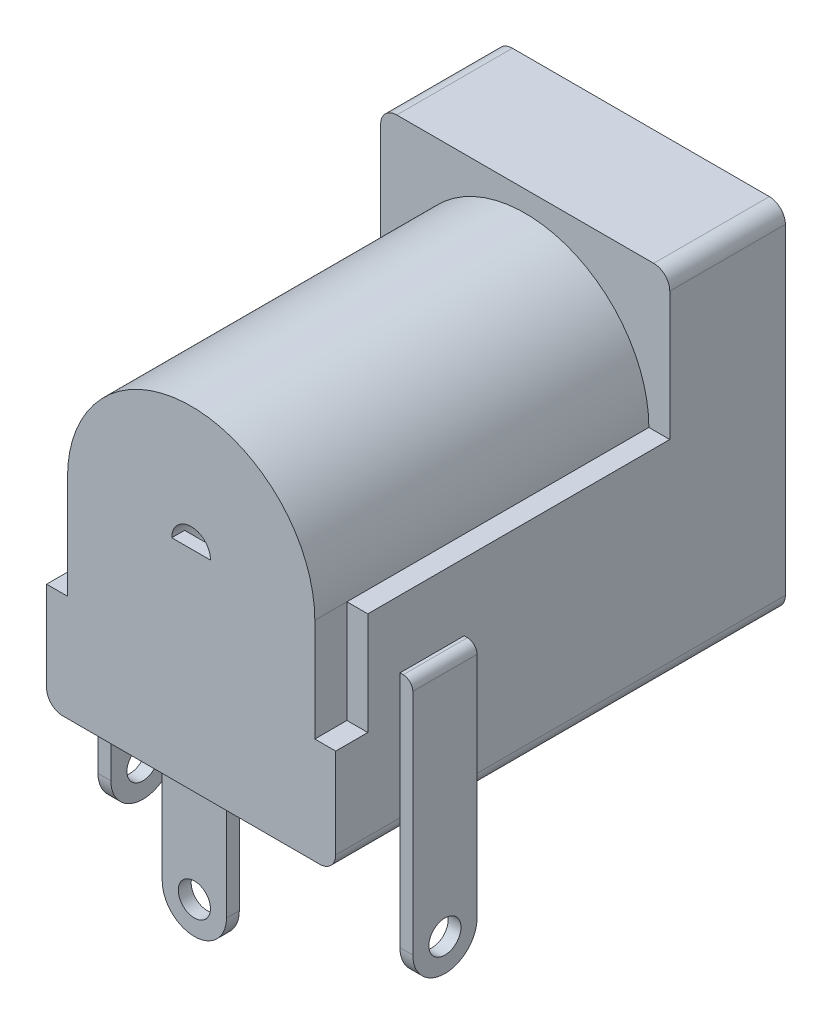
SolidWorks part; units mm, degrees
ref_plane "Front" through (0, 0, 0) normal (0, 0, 1) x (1, 0, 0)
ref_plane "Top" through (0, 0, 0) normal (0, 1, 0) x (1, 0, 0)
ref_plane "Right" through (0, 0, 0) normal (1, 0, 0) x (0, 0, -1)
sketch "草图1" plane through (0, 0, 0) normal (0, 0, 1) x (1, 0, 0)
  line L1 (-4, 5.5) -> (4, 5.5)
  line L2 (-4.5, 5) -> (-4.5, -5)
  line L3 (-4, -5.5) -> (4, -5.5)
  line L4 (4.5, 5) -> (4.5, -5)
  line L5 (-4.5, 5.5) -> (4.5, -5.5) construction
  line L6 (-4.5, -5.5) -> (4.5, 5.5) construction
  arc A0 (-4.5, -5) -> (-4, -5.5) centre (-4, -5) ccw
  arc A1 (4, -5.5) -> (4.5, -5) centre (4, -5) ccw
  arc A2 (4, 5.5) -> (4.5, 5) centre (4, 5) cw
  arc A3 (-4, 5.5) -> (-4.5, 5) centre (-4, 5) ccw
  circle A4 centre (0, 1) radius 3.2
  point P0 (0, 0)
  point P18 (0, 1)
  dimension "D3" = 0.5
  dimension "D1" = 9
  dimension "D2" = 11
  dimension "D4" = 6.5
extrude "凸台-拉伸1" add sketch "草图1" along normal blind 14
sketch "草图2" plane through (0, 0, 14) normal (0, 0, 1) x (1, 0, 0)
  line L0 (3.85, 1) -> (4.5, 1)
  line L1 (4.5, -5) -> (4.5, 5) construction
  line L2 (-3.85, 1) -> (-4.5, 1)
  line L3 (-4.5, 5) -> (-4.5, -5) construction
  line L4 (-4.5, 5) -> (-4.5, 1)
  line L5 (4.5, 1) -> (4.5, 5)
  arc A1 (4.5, 5) -> (4, 5.5) centre (4, 5) ccw construction
  arc A2 (-4, 5.5) -> (-4.5, 5) centre (-4, 5) ccw construction
  arc A3 (4.5, 5) -> (4, 5.5) centre (4, 5) ccw
  arc A4 (-4, 5.5) -> (-4.5, 5) centre (-4, 5) ccw
  arc A6 (-3.85, 1) -> (3.85, 1) centre (0, 1) cw
extrude "切除-拉伸1" cut sketch "草图2" against normal blind 10.4 and the other way through all
sketch "草图3" plane through (0, 0, 14) normal (0, 0, 1) x (1, 0, 0)
  line L0 (-3.85, 1) -> (-3.85, -2.2)
  line L1 (-3.85, -2.2) -> (-4.5, -2.2)
  line L2 (-4.5, 1) -> (-4.5, -5) construction
  line L3 (-4.5, -2.2) -> (-4.5, 1)
  line L4 (-4.5, 1) -> (-3.85, 1)
  line L5 (3.85, 1) -> (3.85, -2.2)
  line L6 (3.85, -2.2) -> (4.5, -2.2)
  line L7 (4.5, -5) -> (4.5, 1) construction
  line L8 (4.5, -2.2) -> (4.5, 1)
  line L9 (4.5, 1) -> (3.85, 1)
extrude "切除-拉伸2" cut sketch "草图3" against normal blind 1
sketch "草图4" plane through (0, -5.5, 0) normal (0, -1, 0) x (-1, 0, 0)
  line L0 (4, 0) -> (-4, 0) construction
  line L1 (0, -11) -> (0, -4.7152) construction
  line L2 (4.5, -12) -> (4.9, -12)
  line L3 (4.5, -12) -> (4.5, -10)
  line L4 (4.5, -10) -> (4.9, -10)
  line L5 (4.9, -12) -> (4.9, -10)
  line L6 (4.5, -12) -> (4.9, -10) construction
  line L7 (4.5, -10) -> (4.9, -12) construction
  line L8 (-4.5, -10) -> (-4.9, -10)
  line L9 (-4.9, -12) -> (-4.9, -10)
  line L10 (-4.5, -12) -> (-4.9, -12)
  line L11 (-4.5, -12) -> (-4.5, -10)
  line L13 (-1, -13.5) -> (1, -13.5)
  line L14 (-1, -13.5) -> (-1, -13.9)
  line L15 (-1, -13.9) -> (1, -13.9)
  line L16 (1, -13.5) -> (1, -13.9)
  line L17 (-1, -13.5) -> (1, -13.9) construction
  line L18 (-1, -13.9) -> (1, -13.5) construction
  point P0 (4.7, -11)
  point P4 (4.7, -11)
  point P15 (0, -13.7)
  point P16 (0, -13.7)
  dimension "D1" = 4.7
  dimension "D2" = 11
  dimension "D3" = 2
  dimension "D4" = 0.4
  dimension "D5" = 13.7
  dimension "D6" = 2
  dimension "D7" = 0.4
extrude "凸台-拉伸2" add sketch "草图4" along normal blind 4 separate body
sketch "草图5" plane through (0, 0, 10) normal (0, 0, -1) x (-1, 0, 0)
  line L0 (4.5, -5.5) -> (4.5, -1.0922)
  line L1 (4.5, 5) -> (4.5, -5) construction
  line L2 (4.5, -1.0922) -> (4.6, -1.0922)
  line L3 (4.9, -1.3922) -> (4.9, -5.5)
  line L4 (4.9, -5.5) -> (4.5, -5.5)
  line L5 (0, 1.7155) -> (0, -4.0055) construction
  line L6 (-4.9, -1.3922) -> (-4.9, -5.5)
  line L7 (-4.5, -1.0922) -> (-4.6, -1.0922)
  line L8 (-4.5, -5.5) -> (-4.5, -1.0922)
  line L9 (-4.9, -5.5) -> (-4.5, -5.5)
  arc A0 (4.6, -1.0922) -> (4.9, -1.3922) centre (4.6, -1.3922) cw
  arc A1 (-4.6, -1.0922) -> (-4.9, -1.3922) centre (-4.6, -1.3922) ccw
  dimension "D1" = 0.3
extrude "凸台-拉伸3" add sketch "草图5" against normal blind 2
sketch "草图7" plane through (-1, 0, 0) normal (-1, 0, 0) x (0, 0, 1)
  line L0 (14, -5.5) -> (14, 1)
  line L1 (14, 1) -> (13.6, 1)
  line L2 (13.9, 0.7) -> (13.9, -5.5)
  line L3 (13.9, -5.5) -> (14, -5.5)
  arc A0 (13.6, 1) -> (13.9, 0.7) centre (13.6, 0.7) cw
  dimension "D1" = 0.3
extrude "凸台-拉伸4" add sketch "草图7" against normal blind 2
sketch "草图8" plane through (0, 0, 14) normal (0, 0, 1) x (1, 0, 0)
  line L0 (-1, 1) -> (1, 1) construction
  circle A0 centre (0, 1) radius 3.2
  circle A1 centre (0, 1) radius 0.6036
extrude "凸台-拉伸5" add sketch "草图8" against normal blind 2
sketch "草图9" plane through (-4.9, 0, 0) normal (-1, 0, 0) x (0, 0, 1)
  line L0 (12, -9.5) -> (10, -9.5) construction
  line L1 (10, -9.5) -> (10, -1.3922) construction
  line L2 (12, -9.5) -> (12, -1.3922) construction
  line L3 (10, -8.5) -> (10, -9.8053)
  line L4 (10, -9.8053) -> (12, -9.8053)
  line L5 (12, -9.8053) -> (12, -8.5)
  arc A0 (10, -8.5) -> (12, -8.5) centre (11, -8.5) ccw
  circle A1 centre (11, -8.5) radius 0.5
  point P0 (11, -8.5)
  dimension "D1" = 1
extrude "切除-拉伸3" cut sketch "草图9" against normal through all
sketch "草图10" plane through (0, 0, 13.9) normal (0, 0, 1) x (1, 0, 0)
  line L0 (1, -9.5) -> (-1, -9.5) construction
  line L1 (-1, -9.5) -> (-1, -5.5) construction
  line L2 (1, -9.5) -> (1, -5.5) construction
  line L3 (-1, -8.5) -> (-1, -10.3598)
  line L4 (-1, -10.3598) -> (1, -10.3598)
  line L5 (1, -10.3598) -> (1, -8.5)
  circle A0 centre (0, -8.5) radius 0.5
  arc A1 (-1, -8.5) -> (1, -8.5) centre (0, -8.5) ccw
  dimension "D1" = 1
extrude "切除-拉伸4" cut sketch "草图10" against normal blind 2
